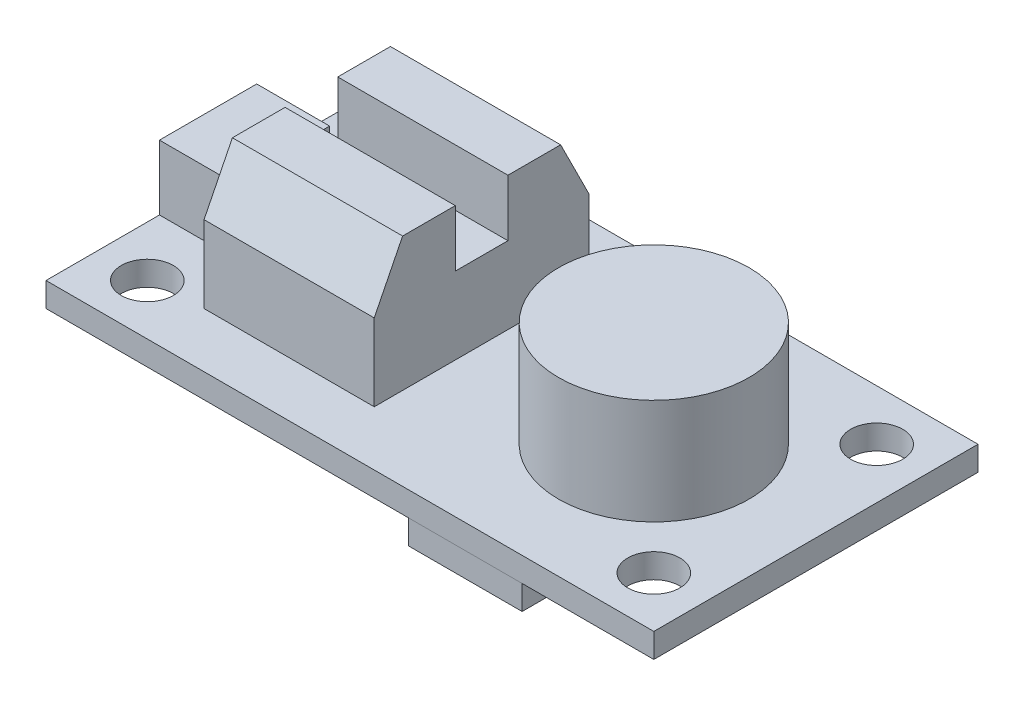
SolidWorks part; units mm, degrees
ref_plane "Front Plane" through (0, 0, 0) normal (0, 0, 1) x (1, 0, 0)
ref_plane "Top Plane" through (0, 0, 0) normal (0, 1, 0) x (1, 0, 0)
ref_plane "Right Plane" through (0, 0, 0) normal (1, 0, 0) x (0, 0, -1)
sketch "Sketch1" plane through (0, 0, 0) normal (0, 1, 0) x (1, 0, 0)
  line L1 (19.05, -10.16) -> (-19.05, -10.16)
  line L2 (19.05, -10.16) -> (19.05, 10.16)
  line L3 (19.05, 10.16) -> (-19.05, 10.16)
  line L4 (-19.05, -10.16) -> (-19.05, 10.16)
  line L5 (19.05, -10.16) -> (-19.05, 10.16) construction
  line L6 (19.05, 10.16) -> (-19.05, -10.16) construction
  point P0 (0, 0)
  dimension "D1" = 38.1
  dimension "D2" = 20.32
extrude "Boss-Extrude1" add sketch "Sketch1" along normal blind 1.524
hole_wizard "#4 Clearance Hole1" positions "Sketch2" profile "Sketch3" hole size "#4" standard "ANSI Inch" end condition through all
sketch "Sketch2" plane through (0, 1.524, 0) normal (0, 1, 0) x (1, 0, 0)
  line L9 (-15.875, 6.985) -> (15.875, 6.985)
  line L10 (-15.875, 6.985) -> (-15.875, -6.985)
  line L11 (-15.875, -6.985) -> (15.875, -6.985)
  line L12 (15.875, 6.985) -> (15.875, -6.985)
  line L13 (19.05, -10.16) -> (19.05, 10.16) construction
  line L14 (19.05, 10.16) -> (-19.05, 10.16) construction
  line L15 (-19.05, 10.16) -> (-19.05, -10.16) construction
  line L16 (-19.05, -10.16) -> (19.05, -10.16) construction
  point P66 (-15.875, 6.985)
  point P67 (15.875, -6.985)
  point P70 (-15.875, -6.985)
  point P71 (15.875, 6.985)
  dimension "D1" = 3.175
  dimension "D2" = 3.175
  dimension "D3" = 3.175
  dimension "D4" = 3.175
sketch "Sketch3" plane through (-15.875, 1.524, -6.985) normal (1, 0, 0) x (0, 0, 1)
  line L0 (0, 0) -> (0, 1.524)
  line L1 (0, 1.524) -> (1.6319, 1.524)
  line L2 (1.6319, 1.524) -> (1.6319, 0)
  line L5 (1.6319, 0) -> (0, 0)
  line L11 (0, -6.35) -> (0, 107.95) construction
  dimension "Thru Hole Dia." = 3.2639
  dimension "Thru Hole Depth" = 1.524
sketch "Sketch4" plane through (0, 1.524, 0) normal (0, 1, 0) x (1, 0, 0)
  line L0 (-19.05, 10.16) -> (-19.05, -10.16) construction
  line L1 (-19.05, 3.048) -> (-14.478, 3.048)
  line L2 (-19.05, 3.048) -> (-19.05, -3.048)
  line L3 (-19.05, -3.048) -> (-14.478, -3.048)
  line L4 (-14.478, 3.048) -> (-14.478, -3.048)
  point P6 (-14.478, 0)
  dimension "D1" = 6.096
  dimension "D2" = 4.572
extrude "Boss-Extrude2" add sketch "Sketch4" along normal blind 4.064
sketch "Sketch5" plane through (0, 1.524, 0) normal (0, 1, 0) x (1, 0, 0)
  line L0 (19.05, -10.16) -> (19.05, 10.16) construction
  circle A0 centre (8.89, 0) radius 5.969
  dimension "D1" = 10.16
  dimension "D2" = 11.938
extrude "Boss-Extrude3" add sketch "Sketch5" along normal blind 6.604
sketch "Sketch6" plane through (0, 1.524, 0) normal (0, 1, 0) x (1, 0, 0)
  line L1 (-1.905, -6.731) -> (-12.573, -6.731)
  line L2 (-1.905, -6.731) -> (-1.905, 6.731)
  line L3 (-1.905, 6.731) -> (-12.573, 6.731)
  line L4 (-12.573, -6.731) -> (-12.573, 6.731)
  line L5 (-1.905, -6.731) -> (-12.573, 6.731) construction
  line L6 (-1.905, 6.731) -> (-12.573, -6.731) construction
  circle A1 centre (8.89, 0) radius 5.969 construction
  point P0 (-7.239, 0)
  dimension "D1" = 13.462
  dimension "D2" = 10.668
  dimension "D3" = 4.826
extrude "Boss-Extrude4" add sketch "Sketch6" along normal blind 4.826
sketch "Sketch7" plane through (-12.573, 0, 0) normal (-1, 0, 0) x (0, 0, 1)
  line L1 (-6.731, 6.35) -> (-4.953, 9.906)
  line L6 (0, 0) -> (0, 50000) construction
  line L18 (6.731, 6.35) -> (4.953, 9.906)
  line L19 (-4.953, 9.906) -> (-1.651, 9.906)
  line L20 (4.953, 9.906) -> (1.651, 9.906)
  line L21 (-1.651, 9.906) -> (-1.651, 6.35)
  line L22 (-6.731, 6.35) -> (6.731, 6.35) construction
  line L23 (1.651, 9.906) -> (1.651, 6.35)
  line L24 (-6.731, 6.35) -> (-1.651, 6.35)
  line L25 (6.731, 6.35) -> (1.651, 6.35)
  dimension "D1" = 3.556
  dimension "D2" = 3.302
  dimension "D3" = 3.302
extrude "Boss-Extrude5" add sketch "Sketch7" against normal up to surface (10.668 mm away) up to face at (-1.905, 3.937, 0)
sketch "Sketch8" plane through (0, 0, 0) normal (0, -1, 0) x (1, 0, 0)
  line L0 (19.05, -10.16) -> (-19.05, -10.16) construction
  line L1 (3.302, -10.16) -> (11.176, -10.16)
  line L2 (3.302, -10.16) -> (3.302, -4.572)
  line L3 (3.302, -4.572) -> (11.176, -4.572)
  line L4 (11.176, -10.16) -> (11.176, -4.572)
  line L5 (19.05, 10.16) -> (19.05, -10.16) construction
  dimension "D1" = 5.588
  dimension "D2" = 7.874
  dimension "D3" = 7.874
extrude "Boss-Extrude6" add sketch "Sketch8" along normal blind 3.048
sketch "Sketch9" plane through (0, 0, 0) normal (0, -1, 0) x (1, 0, 0)
  line L0 (-19.05, 10.16) -> (19.05, 10.16) construction
  line L1 (3.683, 10.16) -> (10.795, 10.16)
  line L2 (3.683, 10.16) -> (3.683, 5.08)
  line L3 (3.683, 5.08) -> (10.795, 5.08)
  line L4 (10.795, 10.16) -> (10.795, 5.08)
  line L5 (11.176, -4.572) -> (3.302, -4.572) construction
  point P8 (7.239, -4.572)
  point P9 (7.239, 5.08)
  dimension "D1" = 5.08
  dimension "D2" = 7.112
extrude "Boss-Extrude7" add sketch "Sketch9" along normal blind 1.524
sketch "Sketch10" plane through (0, 0, 0) normal (0, -1, 0) x (1, 0, 0)
  line L0 (10.795, 5.08) -> (10.795, 10.16) construction
  line L1 (14.859, 2.032) -> (12.319, 2.032)
  line L2 (14.859, 2.032) -> (14.859, -2.032)
  line L3 (14.859, -2.032) -> (12.319, -2.032)
  line L4 (12.319, 2.032) -> (12.319, -2.032)
  point P4 (14.859, 0)
  dimension "D1" = 4.064
  dimension "D2" = 2.54
  dimension "D3" = 1.524
extrude "Boss-Extrude8" add sketch "Sketch10" along normal blind 1.016
sketch "Sketch11" plane through (0, 0, 0) normal (0, -1, 0) x (1, 0, 0)
  line L0 (3.683, 10.16) -> (3.683, 5.08) construction
  line L1 (1.651, -2.54) -> (6.731, -2.54)
  line L2 (1.651, -2.54) -> (1.651, 2.54)
  line L3 (1.651, 2.54) -> (6.731, 2.54)
  line L4 (6.731, -2.54) -> (6.731, 2.54)
  line L5 (1.651, -2.54) -> (6.731, 2.54) construction
  line L6 (1.651, 2.54) -> (6.731, -2.54) construction
  point P0 (4.191, 0)
  dimension "D1" = 5.08
  dimension "D2" = 2.032
extrude "Boss-Extrude9" add sketch "Sketch11" along normal blind 1.016
sketch "Sketch12" plane through (0, 0, 0) normal (0, -1, 0) x (1, 0, 0)
  line L0 (-19.05, 10.16) -> (3.683, 10.16) construction
  line L1 (-0.381, 6.096) -> (-4.445, 6.096)
  line L2 (-0.381, 6.096) -> (-0.381, 8.128)
  line L3 (-0.381, 8.128) -> (-4.445, 8.128)
  line L4 (-4.445, 6.096) -> (-4.445, 8.128)
  line L5 (-0.381, 6.096) -> (-4.445, 8.128) construction
  line L6 (-0.381, 8.128) -> (-4.445, 6.096) construction
  line L7 (3.683, 10.16) -> (3.683, 5.08) construction
  point P0 (-2.413, 7.112)
  dimension "D1" = 2.032
  dimension "D2" = 4.064
  dimension "D3" = 2.032
  dimension "D4" = 4.064
extrude "Boss-Extrude10" add sketch "Sketch12" along normal blind 1.016
sketch "Sketch13" plane through (0, 0, 0) normal (0, -1, 0) x (1, 0, 0)
  line L0 (3.302, -4.572) -> (3.302, -10.16) construction
  line L1 (-2.286, -7.62) -> (-5.334, -7.62)
  line L2 (-2.286, -7.62) -> (-2.286, -4.572)
  line L3 (-2.286, -4.572) -> (-5.334, -4.572)
  line L4 (-5.334, -7.62) -> (-5.334, -4.572)
  line L5 (-2.286, -7.62) -> (-5.334, -4.572) construction
  line L6 (-2.286, -4.572) -> (-5.334, -7.62) construction
  line L7 (3.302, -10.16) -> (-19.05, -10.16) construction
  point P0 (-3.81, -6.096)
  dimension "D1" = 3.048
  dimension "D2" = 5.588
  dimension "D3" = 2.54
extrude "Boss-Extrude11" add sketch "Sketch13" along normal blind 0.508
sketch "Sketch14" plane through (0, 0, 0) normal (0, -1, 0) x (1, 0, 0)
  line L0 (-19.05, -10.16) -> (-19.05, 10.16) construction
  line L1 (-11.43, -4.572) -> (-8.382, -4.572)
  line L2 (-11.43, -4.572) -> (-11.43, -8.128)
  line L3 (-11.43, -8.128) -> (-8.382, -8.128)
  line L4 (-8.382, -4.572) -> (-8.382, -8.128)
  line L5 (-11.43, -4.572) -> (-8.382, -8.128) construction
  line L6 (-11.43, -8.128) -> (-8.382, -4.572) construction
  line L7 (3.302, -10.16) -> (-19.05, -10.16) construction
  point P0 (-9.906, -6.35)
  dimension "D1" = 3.556
  dimension "D2" = 3.048
  dimension "D3" = 7.62
  dimension "D4" = 2.032
extrude "Boss-Extrude12" add sketch "Sketch14" along normal blind 1.016
sketch "Sketch15" plane through (0, 0, 0) normal (0, -1, 0) x (1, 0, 0)
  line L0 (3.302, -10.16) -> (-19.05, -10.16) construction
  line L1 (-16.51, 3.302) -> (-14.478, 3.302)
  line L2 (-16.51, 3.302) -> (-16.51, -0.762)
  line L3 (-16.51, -0.762) -> (-14.478, -0.762)
  line L4 (-14.478, 3.302) -> (-14.478, -0.762)
  line L5 (-16.51, 3.302) -> (-14.478, -0.762) construction
  line L6 (-16.51, -0.762) -> (-14.478, 3.302) construction
  line L7 (-19.05, -10.16) -> (-19.05, 10.16) construction
  point P0 (-15.494, 1.27)
  dimension "D1" = 4.064
  dimension "D2" = 2.032
  dimension "D3" = 9.398
  dimension "D4" = 2.54
extrude "Boss-Extrude13" add sketch "Sketch15" along normal blind 1.524
sketch "Sketch16" plane through (0, 0, 0) normal (0, -1, 0) x (1, 0, 0)
  line L0 (-19.05, -10.16) -> (-19.05, 10.16) construction
  line L1 (-7.874, -1.524) -> (-10.922, -1.524)
  line L2 (-7.874, -1.524) -> (-7.874, 1.524)
  line L3 (-7.874, 1.524) -> (-10.922, 1.524)
  line L4 (-10.922, -1.524) -> (-10.922, 1.524)
  line L5 (-7.874, -1.524) -> (-10.922, 1.524) construction
  line L6 (-7.874, 1.524) -> (-10.922, -1.524) construction
  point P0 (-9.398, 0)
  point P8 (-19.05, 0)
  dimension "D1" = 3.048
  dimension "D2" = 8.128
extrude "Boss-Extrude14" add sketch "Sketch16" along normal blind 1.016
sketch "Sketch17" plane through (0, 0, 0) normal (0, -1, 0) x (1, 0, 0)
  line L0 (-19.05, -10.16) -> (-19.05, 10.16) construction
  line L1 (3.302, -10.16) -> (-19.05, -10.16) construction
  circle A0 centre (-11.684, -3.556) radius 0.508
  dimension "D1" = 1.016
  dimension "D2" = 6.858
  dimension "D3" = 6.096
extrude "Boss-Extrude15" add sketch "Sketch17" along normal blind 1.524
pattern_linear "LPattern1" count 4 spacing 2.794 along (1, 0, 0) of "Boss-Extrude15"
mirror "Mirror1" about plane through (0, 0, 0) normal (0, 0, 1) of "LPattern1", "Boss-Extrude15"
sketch "Sketch18" plane through (-19.05, 0, 0) normal (-1, 0, 0) x (0, 0, 1)
  line L0 (-3.048, 1.524) -> (3.048, 1.524)
split line "Split Line1"
sketch "Sketch19" plane through (0, 0, 10.16) normal (0, 0, 1) x (1, 0, 0)
  line L0 (3.683, 0) -> (10.795, 0)
  line L1 (11.176, 0) -> (3.302, 0) construction
  line L2 (10.795, 0) -> (19.05, 0) construction
split line "Split Line2"
sketch "Sketch20" plane through (0, 0, -10.16) normal (0, 0, -1) x (-1, 0, 0)
  line L0 (-11.176, 0) -> (-3.302, 0)
split line "Split Line3"
